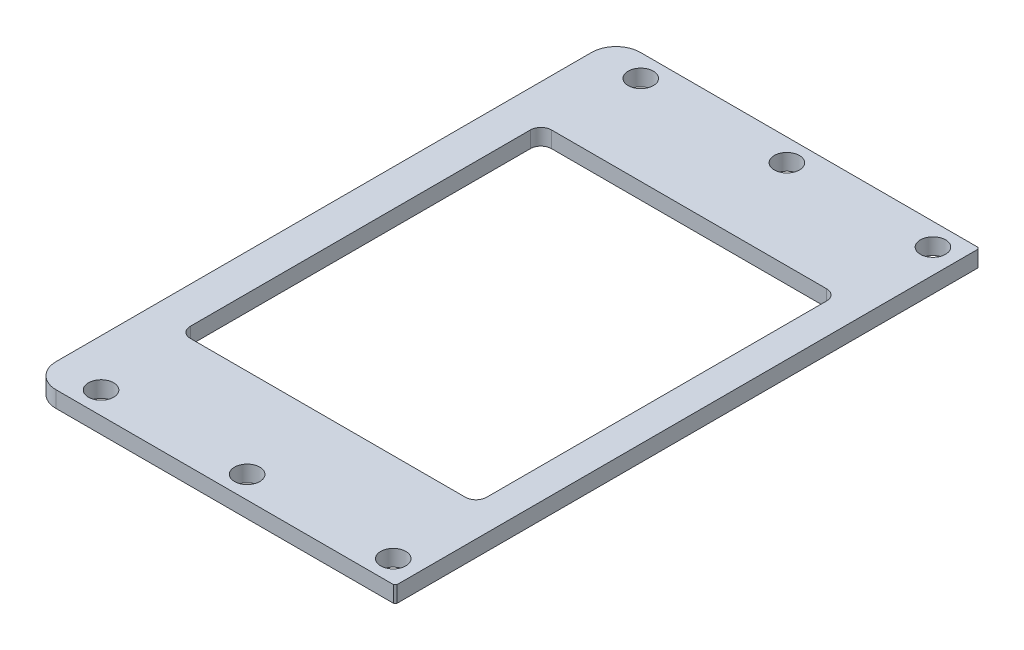
SolidWorks part; units mm, degrees
material "Thornel Mat VMA"
ref_plane "Front Plane" through (0, 0, 0) normal (0, 0, 1) x (1, 0, 0)
ref_plane "Top Plane" through (0, 0, 0) normal (0, 1, 0) x (1, 0, 0)
ref_plane "Right Plane" through (0, 0, 0) normal (1, 0, 0) x (0, 0, -1)
sketch "Sketch1" plane through (0, 0, 0) normal (0, 1, 0) x (1, 0, 0)
  line L0 (-22.4, -33.25) -> (22.4, -33.25) construction
  line L1 (-22.4, -36) -> (22.4, -36)
  line L2 (-22.4, -36) -> (-22.4, 36)
  line L3 (-22.4, 36) -> (22.4, 36)
  line L4 (22.4, -36) -> (22.4, 36)
  line L5 (-22.4, -36) -> (22.4, 36) construction
  line L6 (-22.4, 36) -> (22.4, -36) construction
  line L7 (17.3, -22.25) -> (-16.6, -22.25)
  line L8 (18.6, -20.95) -> (18.6, 20.95)
  line L9 (17.3, 22.25) -> (-16.6, 22.25)
  line L10 (-17.9, -20.95) -> (-17.9, 20.95)
  line L11 (18.6, -22.25) -> (-17.9, 22.25) construction
  line L12 (18.6, 22.25) -> (-17.9, -22.25) construction
  line L19 (-49.3451, 0) -> (49.3451, 0) construction
  arc A0 (-16.6, -22.25) -> (-17.9, -20.95) centre (-16.6, -20.95) cw
  arc A1 (17.3, -22.25) -> (18.6, -20.95) centre (17.3, -20.95) ccw
  arc A2 (18.6, 20.95) -> (17.3, 22.25) centre (17.3, 20.95) ccw
  arc A3 (-16.6, 22.25) -> (-17.9, 20.95) centre (-16.6, 20.95) ccw
  circle A4 centre (-16.6, -33.25) radius 1.55
  circle A5 centre (1.4, -33.25) radius 1.55
  circle A6 centre (19.4, -33.25) radius 1.55
  circle A7 centre (-16.6, 33.25) radius 1.55
  circle A8 centre (1.4, 33.25) radius 1.55
  circle A9 centre (19.4, 33.25) radius 1.55
  point P0 (0, 0)
  point P6 (0.35, 0)
  point P38 (0, 0)
  dimension "D8" = 1.3
  dimension "D10" = 3.1
  dimension "D1" = 44.8
  dimension "D2" = 72
  dimension "D3" = 44.5
  dimension "D4" = 36.5
  dimension "D5" = 1.3
  dimension "D9" = 5.8
  dimension "D11" = 18
  dimension "D12" = 18
  dimension "D13" = 2.75
extrude "Boss-Extrude1" add sketch "Sketch1" along normal blind 2
chamfer "Chamfer2" distance 0.2 angle 45 2 edges at (22.4, 1, -36) (22.4, 1, 36)
fillet "Fillet3" radius 3 2 edges at (-22.4, 1, -36) (-22.4, 1, 36)
